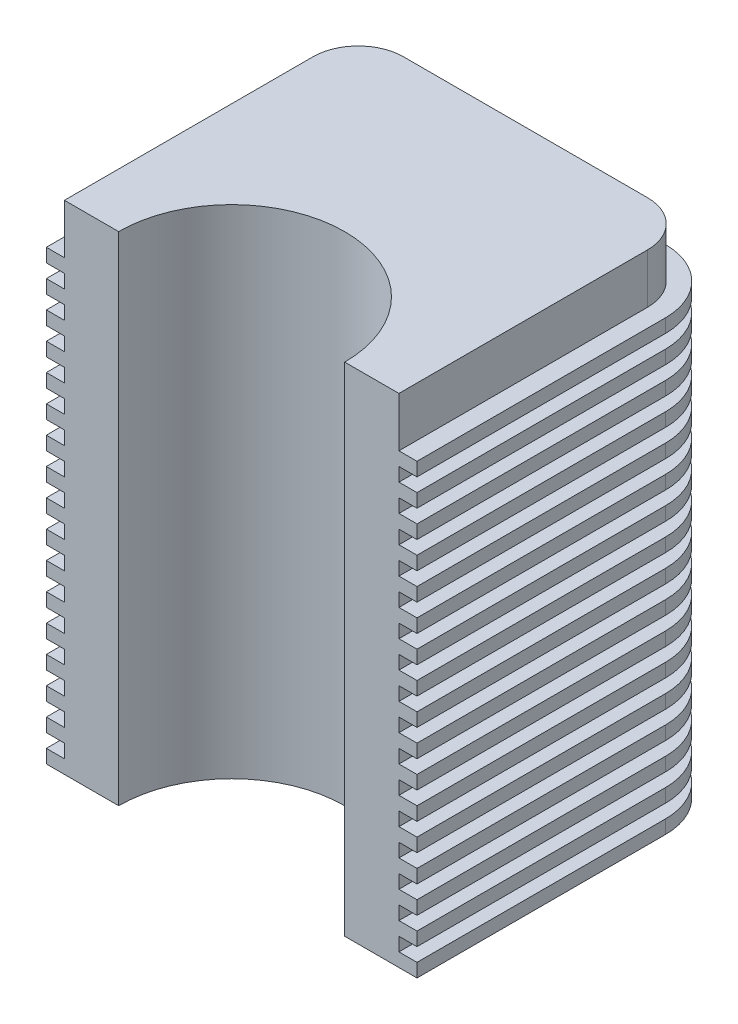
SolidWorks part; units mm, degrees
ref_plane "Front Plane" through (0, 0, 0) normal (0, 0, 1) x (1, 0, 0)
ref_plane "Top Plane" through (0, 0, 0) normal (0, 1, 0) x (1, 0, 0)
ref_plane "Right Plane" through (0, 0, 0) normal (1, 0, 0) x (0, 0, -1)
sketch "Sketch1" plane through (0, 0, 0) normal (0, 1, 0) x (1, 0, 0)
  line L0 (25, 0) -> (37, 0)
  line L1 (37, 0) -> (37, 55)
  line L2 (27, 65) -> (-27, 65)
  line L3 (0, 0) -> (0, 49.4671) construction
  line L4 (-37, 0) -> (-37, 55)
  line L5 (-25, 0) -> (-37, 0)
  arc A0 (25, 0) -> (-25, 0) centre (0, 0) ccw
  arc A1 (37, 55) -> (27, 65) centre (27, 55) ccw
  arc A2 (-27, 65) -> (-37, 55) centre (-27, 55) ccw
  point P9 (0, 65)
  point P13 (37, 65)
  point P16 (-37, 65)
  dimension "D1" = 50
  dimension "D4" = 10
  dimension "D2" = 12
  dimension "D3" = 65
extrude "Boss-Extrude1" add sketch "Sketch1" along normal blind 110
sketch "Sketch2" plane through (0, 0, 0) normal (0, -1, 0) x (1, 0, 0)
  line L5 (-25, 0) -> (-37, 0)
  line L6 (-37, 0) -> (-37, -55)
  line L7 (-27, -65) -> (27, -65)
  line L8 (37, -55) -> (37, 0)
  line L9 (37, 0) -> (25, 0)
  line L10 (-25, 0) -> (-37, 0)
  line L11 (-37, 0) -> (-37, -55)
  line L12 (-27, -65) -> (27, -65)
  line L13 (37, -55) -> (37, 0)
  line L14 (37, 0) -> (25, 0)
  line L15 (-37, 0) -> (-41, 0)
  line L16 (37, 0) -> (41, 0)
  line L20 (-20.6155, 4) -> (-41, 4)
  line L21 (-41, 4) -> (-41, -55)
  line L22 (-27, -69) -> (27, -69)
  line L23 (41, -55) -> (41, 4)
  line L24 (41, 4) -> (20.6155, 4)
  line L26 (-41, 0) -> (-41, -55)
  line L27 (-27, -69) -> (27, -69)
  line L28 (41, -55) -> (41, 0)
  arc A3 (-25, 0) -> (25, 0) centre (0, 0) ccw
  arc A4 (-37, -55) -> (-27, -65) centre (-27, -55) ccw
  arc A5 (27, -65) -> (37, -55) centre (27, -55) ccw
  arc A6 (-25, 0) -> (25, 0) centre (0, 0) ccw
  arc A7 (-37, -55) -> (-27, -65) centre (-27, -55) ccw
  arc A8 (27, -65) -> (37, -55) centre (27, -55) ccw
  arc A12 (-20.6155, 4) -> (20.6155, 4) centre (0, 0) ccw
  arc A13 (-41, -55) -> (-27, -69) centre (-27, -55) ccw
  arc A14 (27, -69) -> (41, -55) centre (27, -55) ccw
  arc A16 (-41, -55) -> (-27, -69) centre (-27, -55) ccw
  arc A17 (27, -69) -> (41, -55) centre (27, -55) ccw
  line M19 (-37, 0) -> (-37, -55)
  arc M20 (-37, -55) -> (-27, -65) centre (-27, -55) ccw
  line M21 (-27, -65) -> (27, -65)
  arc M22 (27, -65) -> (37, -55) centre (27, -55) ccw
  line M23 (37, -55) -> (37, 0)
  dimension "D1" = 0
  dimension "D2" = 4
extrude "Boss-Extrude2" add sketch "Sketch2" against normal blind 3 contours L27 A17 L28 L16 L15 L26 A16 M23 M22 M21 M20 M19
pattern_linear "LPattern1" count 17 spacing 6 along (0, 1, 0) of "Boss-Extrude2"
